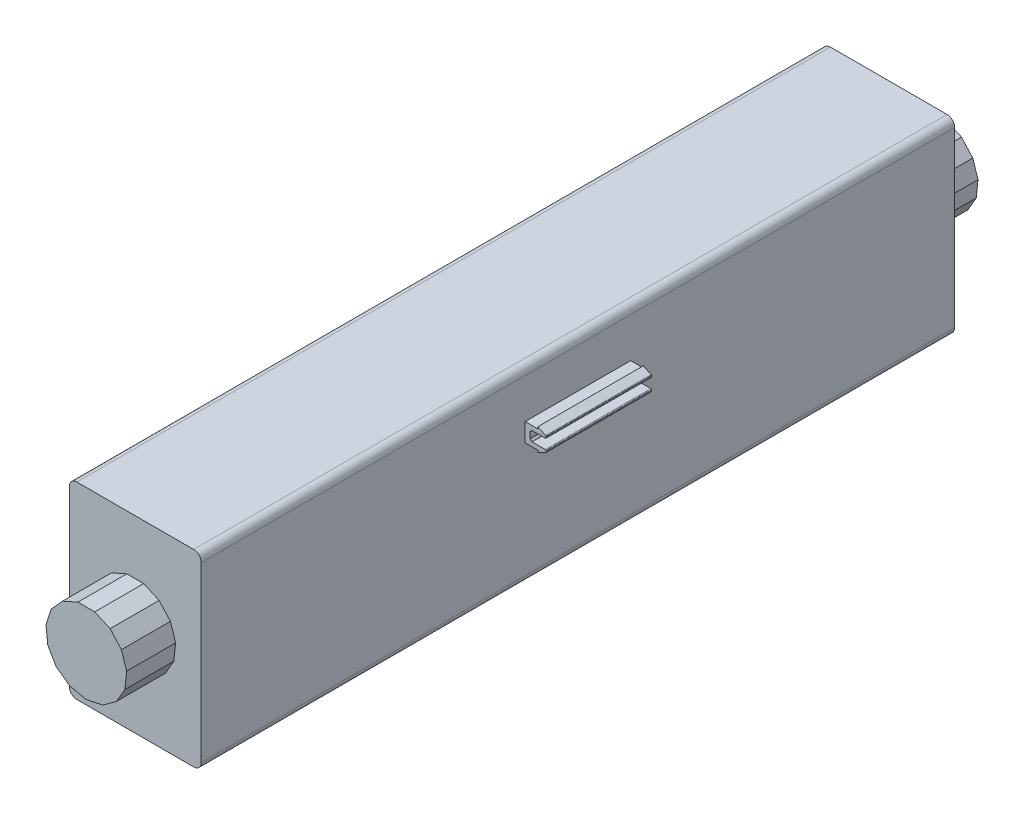
SolidWorks part; units mm, degrees
ref_plane "Front Plane" through (0, 0, 0) normal (0, 0, 1) x (1, 0, 0)
ref_plane "Top Plane" through (0, 0, 0) normal (0, 1, 0) x (1, 0, 0)
ref_plane "Right Plane" through (0, 0, 0) normal (1, 0, 0) x (0, 0, -1)
sketch "Sketch9" plane through (54.2356, 0, 0) normal (0, 0, 1) x (1, 0, 0)
  line L1 (26.6848, -242.8589) -> (22.2106, -242.8589)
  line L2 (22.2106, -242.8589) -> (18.1231, -244.6788)
  line L3 (18.1231, -244.6788) -> (15.1293, -248.0038)
  line L4 (15.1293, -248.0038) -> (13.7466, -252.2591)
  line L5 (13.7466, -252.2591) -> (14.2143, -256.7088)
  line L6 (14.2143, -256.7088) -> (16.4514, -260.5836)
  line L7 (16.4514, -260.5836) -> (20.0712, -263.2136)
  line L8 (20.0712, -263.2136) -> (24.4477, -264.1438)
  line L9 (24.4477, -264.1438) -> (28.8242, -263.2136)
  line L10 (28.8242, -263.2136) -> (32.4439, -260.5836)
  line L11 (32.4439, -260.5836) -> (34.6811, -256.7088)
  line L12 (34.6811, -256.7088) -> (35.1487, -252.2591)
  line L13 (35.1487, -252.2591) -> (33.7661, -248.0038)
  line L14 (33.7661, -248.0038) -> (30.7723, -244.6788)
  line L15 (30.7723, -244.6788) -> (26.6848, -242.8589)
  circle A1 centre (24.4477, -253.3838) radius 10.5249 construction
  dimension "D1" = 10.76
extrude "Boss-Extrude6" add sketch "Sketch9" along normal blind 13
sketch "Sketch10" plane through (0, 0, 13) normal (0, 0, 1) x (1, 0, 0)
  line L5 (61.1833, -228.3838) -> (96.1833, -228.3838)
  line L6 (61.1833, -228.3838) -> (61.1833, -278.3838)
  line L7 (61.1833, -278.3838) -> (96.1833, -278.3838)
  line L8 (96.1833, -228.3838) -> (96.1833, -278.3838)
  line L9 (61.1833, -228.3838) -> (96.1833, -278.3838) construction
  line L10 (61.1833, -278.3838) -> (96.1833, -228.3838) construction
  dimension "D1" = 35
  dimension "D2" = 50
extrude "Boss-Extrude7" add sketch "Sketch10" along normal blind 200
sketch "Sketch11" plane through (0, 0, 213) normal (0, 0, 1) x (1, 0, 0)
  line L0 (61.1833, -228.3838) -> (96.1833, -278.3838)
  line L6 (61.1833, -228.3838) -> (96.1833, -228.3838)
  line L37 (61.1833, -228.3838) -> (61.1833, -278.3838)
  line L38 (61.1833, -278.3838) -> (96.1833, -278.3838)
  line L39 (96.1833, -228.3838) -> (96.1833, -278.3838)
  line L40 (61.1833, -278.3838) -> (96.1833, -228.3838)
  line L42 (78.6833, -264.1438) -> (83.0598, -263.2136)
  line L43 (83.0598, -263.2136) -> (86.6795, -260.5836)
  line L44 (86.6795, -260.5836) -> (88.9166, -256.7088)
  line L45 (88.9166, -256.7088) -> (89.3843, -252.2591)
  line L46 (89.3843, -252.2591) -> (88.0017, -248.0038)
  line L47 (88.0017, -248.0038) -> (85.0078, -244.6788)
  line L48 (85.0078, -244.6788) -> (80.9204, -242.8589)
  line L49 (80.9204, -242.8589) -> (76.4461, -242.8589)
  line L50 (76.4461, -242.8589) -> (72.3587, -244.6788)
  line L51 (72.3587, -244.6788) -> (69.3648, -248.0038)
  line L52 (69.3648, -248.0038) -> (67.9822, -252.2591)
  line L53 (67.9822, -252.2591) -> (68.4499, -256.7088)
  line L54 (68.4499, -256.7088) -> (70.687, -260.5836)
  line L55 (70.687, -260.5836) -> (74.3068, -263.2136)
  line L56 (74.3068, -263.2136) -> (78.6833, -264.1438)
  circle A0 centre (78.6833, -253.3838) radius 10.5249 construction
  dimension "D1" = 10.76
extrude "Boss-Extrude8" add sketch "Sketch11" along normal blind 13
sketch "Sketch12" plane through (0, 0, 213) normal (0, 0, 1) x (1, 0, 0)
  line L4 (99.547, -240.9763) -> (99.547, -240.4763)
  line L5 (99.547, -246.3763) -> (101.7389, -245.3298)
  line L6 (101.7389, -244.7263) -> (97.9972, -244.7263)
  line L7 (101.7389, -242.1263) -> (101.7389, -241.5242)
  line L8 (97.497, -242.6264) -> (97.997, -242.1263)
  line L9 (97.497, -242.6264) -> (97.497, -244.2344)
  line L10 (97.497, -244.2344) -> (97.9972, -244.7263)
  line L11 (101.7389, -242.1263) -> (97.997, -242.1263)
  line L12 (101.7389, -244.7263) -> (101.7389, -245.3298)
  line L13 (99.547, -246.3763) -> (99.547, -245.8763)
  line L17 (99.547, -240.4763) -> (101.7389, -241.5242)
  line L18 (96.1833, -228.3838) -> (96.1833, -278.3838)
  line L19 (99.547, -240.9763) -> (96.1833, -240.9763)
  line L20 (99.547, -245.8763) -> (96.1833, -245.8763)
extrude "Boss-Extrude10" add sketch "Sketch12" against normal blind 200
fillet "Fillet2" radius 0.2 7 edges at (101.7389, -242.1263, 113) (97.497, -242.6264, 113) (97.497, -244.2344, 113) (97.9972, -244.7263, 113) (97.997, -242.1263, 113) (101.7389, -245.3298, 113) (101.7389, -241.5242, 113)
fillet "Fillet3" radius 0.2 1 edges at (101.7389, -244.7263, 113)
sketch "Sketch13" plane through (0, -240.9763, 0) normal (0, 1, 0) x (1, 0, 0)
  line L0 (96.1833, -113) -> (96.1833, -99)
  line L1 (96.1833, -13) -> (96.1833, -213) construction
  line L2 (96.1833, -113) -> (96.1833, -127)
  line L3 (96.1833, -13) -> (96.1833, -213)
  line L4 (96.1833, -99) -> (165.6747, -99)
  line L5 (96.1833, -99) -> (96.1833, -3.9756)
  line L6 (96.1833, -3.9756) -> (165.6747, -3.9756)
  line L7 (165.6747, -99) -> (165.6747, -3.9756)
  line L8 (96.1833, -127) -> (167.1754, -127)
  line L9 (96.1833, -127) -> (96.1833, -247)
  line L10 (96.1833, -247) -> (167.1754, -247)
  line L11 (167.1754, -127) -> (167.1754, -247)
  dimension "D1" = 14
  dimension "D2" = 14
  dimension "D3" = 120
extrude "Cut-Extrude1" cut sketch "Sketch13" against normal blind 40 and the other way blind 40 contours L9 L10 L11 L8 | L4 L7 L6 L5
fillet "Fillet4" radius 2 4 edges at (61.1833, -278.3838, 113) (96.1833, -278.3838, 113) (96.1833, -228.3838, 113) (61.1833, -228.3838, 113)
